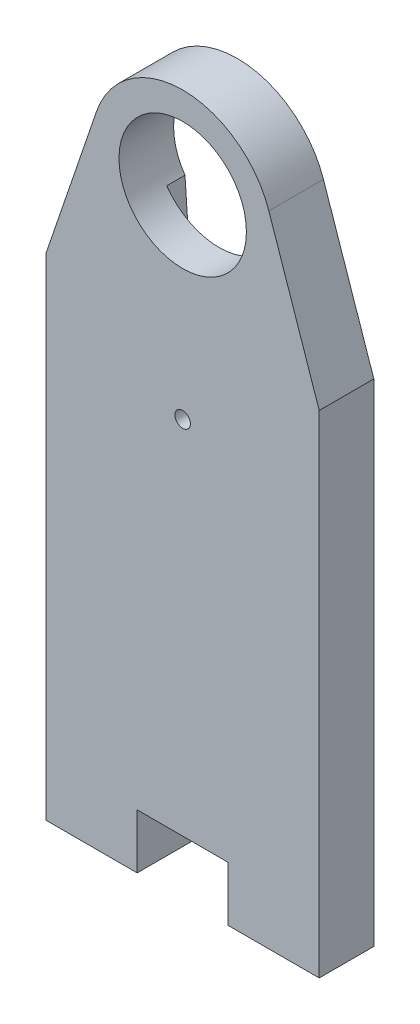
SolidWorks part; units mm, degrees
ref_plane "Alzado" through (0, 0, 0) normal (0, 0, 1) x (1, 0, 0)
ref_plane "Planta" through (0, 0, 0) normal (0, 1, 0) x (1, 0, 0)
ref_plane "Vista lateral" through (0, 0, 0) normal (1, 0, 0) x (0, 0, -1)
sketch "Corte exterior" plane through (0, 0, 0) normal (0, 0, 1) x (1, 0, 0)
  line L0 (40.0158, -3.3108) -> (40.0158, 10.6892)
  line L1 (40.0158, 10.6892) -> (40.0158, 23.6892)
  line L2 (37.2481, 31.8034) -> (40.0158, 23.6892)
  line L3 (25.0158, 23.6892) -> (27.7835, 31.8034)
  line L4 (25.0158, -3.3108) -> (25.0158, 23.6892)
  line L5 (30.0158, -3.3108) -> (25.0158, -3.3108)
  line L6 (30.0158, -0.3108) -> (30.0158, -3.3108)
  line L7 (35.0158, -0.3108) -> (30.0158, -0.3108)
  line L8 (35.0158, -3.3108) -> (35.0158, -0.3108)
  line L9 (40.0158, -3.3108) -> (35.0158, -3.3108)
  circle A0 centre (32.5158, 19.517) radius 0.425
  circle A1 centre (32.5158, 30.1892) radius 3.5
  arc A2 (37.2481, 31.8034) -> (27.7835, 31.8034) centre (32.5158, 30.1892) ccw
sketch "Grabado Superficie" plane through (0, 0, 0) normal (0, 0, 1) x (1, 0, 0)
  line L0 (30.5206, 15.5504) -> (29.6408, 28.1931)
  line L1 (35.3908, 28.1931) -> (34.511, 15.5504)
  arc A0 (29.6408, 28.1931) -> (35.3908, 28.1931) centre (32.5158, 30.1892) ccw
  arc A1 (30.5206, 15.5504) -> (34.511, 15.5504) centre (32.5158, 15.6892) ccw
extrude "Saliente-Extruir1" add sketch "Corte exterior" along normal blind 3
extrude "Cortar-Extruir1" cut sketch "Grabado Superficie" along normal blind 1
